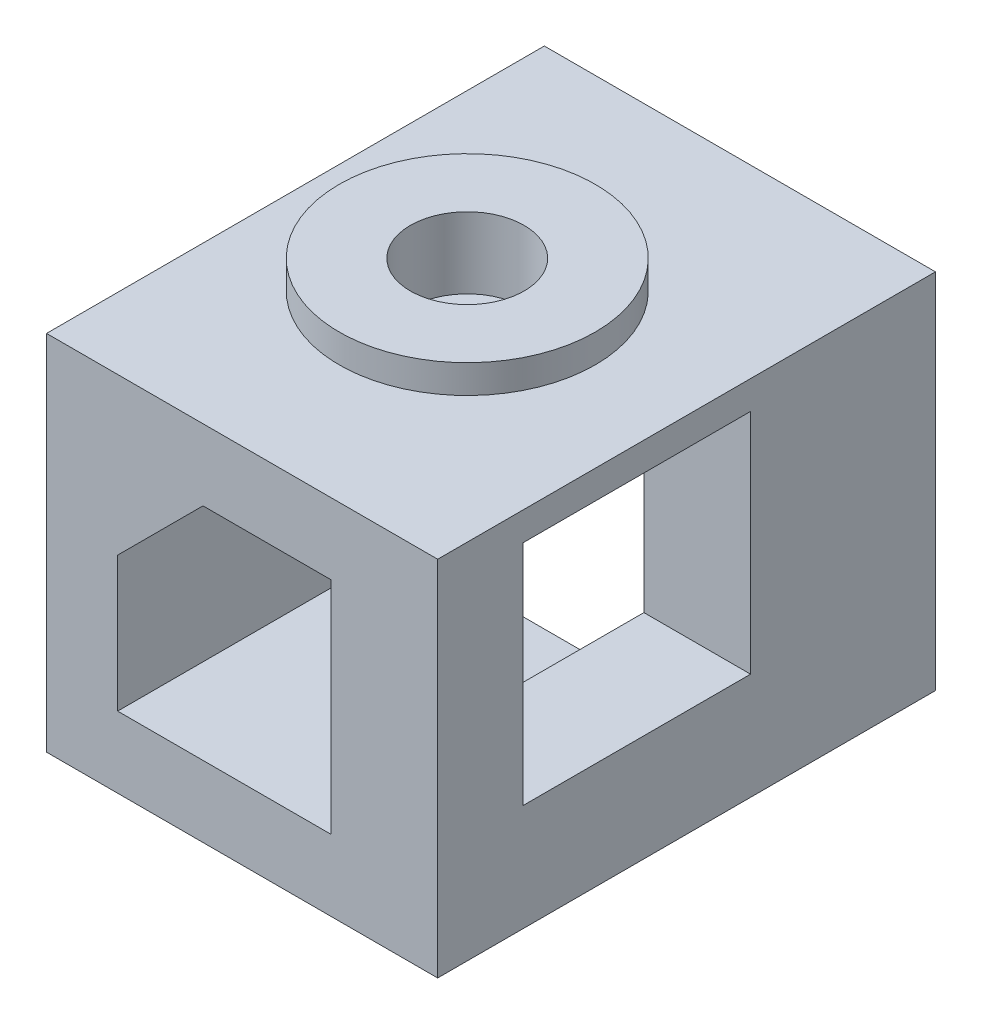
SolidWorks part; units mm, degrees
ref_plane "Front Plane" through (0, 0, 0) normal (0, 0, 1) x (1, 0, 0)
ref_plane "Top Plane" through (0, 0, 0) normal (0, 1, 0) x (1, 0, 0)
ref_plane "Right Plane" through (0, 0, 0) normal (1, 0, 0) x (0, 0, -1)
sketch "Sketch1" plane through (0, 0, 0) normal (0, 0, 1) x (1, 0, 0)
  line L0 (-9.3056, 4.7356) -> (18.1944, 4.7356)
  line L1 (18.1944, 4.7356) -> (18.1944, -0.2644)
  line L2 (18.1944, -0.2644) -> (1.6944, -0.2644)
  line L3 (1.6944, -0.2644) -> (-4.3056, -6.2644)
  line L4 (-4.3056, -6.2644) -> (-4.3056, -13.2644)
  line L5 (-4.3056, -13.2644) -> (-9.3056, -13.2644)
  line L6 (-9.3056, -13.2644) -> (-9.3056, 4.7356)
  line L7 (-4.3056, -6.2644) -> (-4.3056, -0.2644) construction
  line L8 (-4.3056, -0.2644) -> (1.6944, -0.2644) construction
  dimension "D1" = 18
  dimension "D2" = 27.5
  dimension "D3" = 5
  dimension "D4" = 5
  dimension "D5" = 6
  dimension "D6" = 6
extrude "Boss-Extrude1" add sketch "Sketch1" along normal blind 35
sketch "Sketch2" plane through (0, 4.7356, 0) normal (0, 1, 0) x (1, 0, 0)
  line L0 (-9.3056, -35) -> (-9.3056, 0) construction
  line L1 (18.1944, 0) -> (-9.3056, 0) construction
  circle A0 centre (2.9044, -17.63) radius 9
  dimension "D1" = 18
  dimension "D2" = 12.21
  dimension "D3" = 17.63
extrude "Boss-Extrude2" add sketch "Sketch2" along normal blind 2
sketch "Sketch3" plane through (0, 6.7356, 0) normal (0, 1, 0) x (1, 0, 0)
  circle A0 centre (2.9044, -17.63) radius 4
  dimension "D1" = 8
extrude "Cut-Extrude1" cut sketch "Sketch3" against normal blind 5
sketch "Sketch4" plane through (0, -0.2644, 0) normal (0, -1, 0) x (1, 0, 0)
  line L0 (1.6944, 35) -> (18.1944, 35) construction
  line L1 (18.1944, 35) -> (10.6944, 35)
  line L2 (18.1944, 35) -> (18.1944, 0)
  line L3 (18.1944, 0) -> (10.6944, 0)
  line L4 (10.6944, 35) -> (10.6944, 0)
  line L5 (18.1944, 35) -> (18.1944, 0) construction
  line L6 (1.6944, 0) -> (18.1944, 0) construction
  dimension "D1" = 7.5
extrude "Boss-Extrude3" add sketch "Sketch4" along normal blind 20.5
sketch "Sketch6" plane through (18.1944, 0, 0) normal (1, 0, 0) x (0, 0, -1)
  line L0 (-35, 4.7356) -> (0, 4.7356) construction
  line L1 (0, -20.7644) -> (-5, -20.7644)
  line L2 (0, -20.7644) -> (0, 4.7356)
  line L3 (0, 4.7356) -> (-5, 4.7356)
  line L4 (-5, -20.7644) -> (-5, 4.7356)
  dimension "D1" = 5
extrude "Boss-Extrude4" add sketch "Sketch6" along normal blind 7.5 from surface at -7.5 starting at face at (10.6944, -10.5144, 17.5)
sketch "Sketch7" plane through (0, -13.2644, 0) normal (0, -1, 0) x (1, 0, 0)
  line L0 (-4.3056, 35) -> (-4.3056, 0) construction
  line L1 (-9.3056, 35) -> (-4.3056, 35)
  line L2 (-9.3056, 35) -> (-9.3056, 15)
  line L3 (-9.3056, 15) -> (-4.3056, 15)
  line L4 (-4.3056, 35) -> (-4.3056, 15)
  dimension "D1" = 20
extrude "Boss-Extrude5" add sketch "Sketch7" along normal up to surface (7.5 mm away) up to face at (14.4444, -20.7644, 17.5)
sketch "Sketch8" plane through (-4.3056, 0, 0) normal (1, 0, 0) x (0, 0, -1)
  line L0 (-15, -20.7644) -> (-15, -13.2644) construction
  line L1 (-35, -20.7644) -> (-15, -20.7644)
  line L2 (-35, -20.7644) -> (-35, -15.7644)
  line L3 (-35, -15.7644) -> (-15, -15.7644)
  line L4 (-15, -20.7644) -> (-15, -15.7644)
  dimension "D1" = 5
extrude "Boss-Extrude6" add sketch "Sketch8" along normal up to surface (15 mm away) up to face at (10.6944, -10.5144, 17.5)
sketch "Sketch10" plane through (18.1944, 0, 0) normal (1, 0, 0) x (0, 0, -1)
  line L0 (-35, 4.7356) -> (0, 4.7356) construction
  line L1 (-29, 2.7356) -> (-13, 2.7356)
  line L2 (-29, 2.7356) -> (-29, -13.2644)
  line L3 (-29, -13.2644) -> (-13, -13.2644)
  line L4 (-13, 2.7356) -> (-13, -13.2644)
  line L5 (-29, 2.7356) -> (-13, -13.2644) construction
  line L6 (-29, -13.2644) -> (-13, 2.7356) construction
  line L7 (-35, -20.7644) -> (-35, 4.7356) construction
  point P0 (-21, -5.2644)
  dimension "D1" = 16
  dimension "D2" = 16
  dimension "D3" = 10
  dimension "D4" = 14
extrude "Cut-Extrude2" cut sketch "Sketch10" against normal up to surface (7.5 mm away) up to face at (10.6944, -12.2644, 16.6667)
